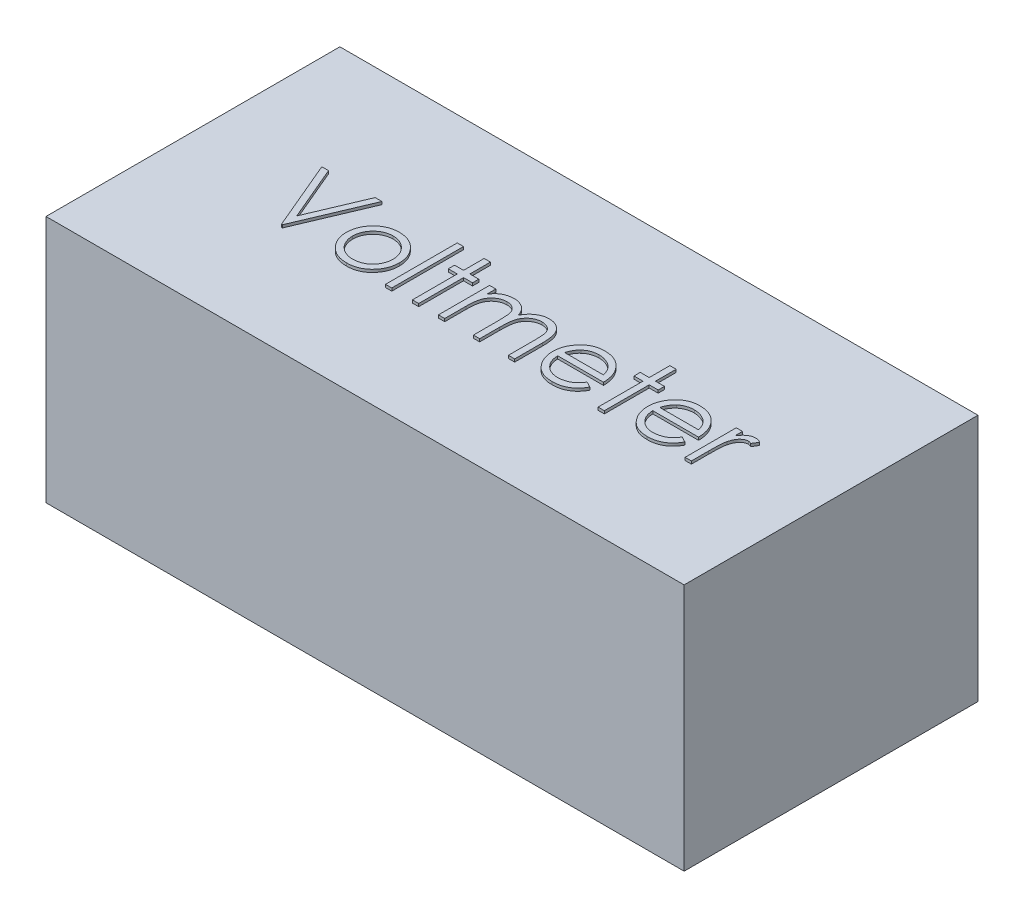
SolidWorks part; units mm, degrees
ref_plane "Front Plane" through (0, 0, 0) normal (0, 0, 1) x (1, 0, 0)
ref_plane "Top Plane" through (0, 0, 0) normal (0, 1, 0) x (1, 0, 0)
ref_plane "Right Plane" through (0, 0, 0) normal (1, 0, 0) x (0, 0, -1)
sketch "Sketch1" plane through (0, 0, 0) normal (0, 1, 0) x (1, 0, 0)
  line L1 (-14.0685, -2.1021) -> (8.7315, -2.1021)
  line L2 (-14.0685, -2.1021) -> (-14.0685, 8.3979)
  line L3 (-14.0685, 8.3979) -> (8.7315, 8.3979)
  line L4 (8.7315, -2.1021) -> (8.7315, 8.3979)
  dimension "D1" = 22.8
  dimension "D2" = 10.5
extrude "Boss-Extrude1" add sketch "Sketch1" along normal blind 8.86
sketch "Sketch2" plane through (0, 8.86, 0) normal (0, 1, 0) x (1, 0, 0)
  text T0 "Voltmeter" font "Century Gothic" height 2.5
  point P1 (-13.234, -0.8387)
  point P2 (-13.6832, -0.7826)
  point P3 (-14.0685, -0.9697)
  point P4 (-11.4559, 1.033)
  point P5 (-10.7447, 1.1827)
  point P6 (-14.0685, 1.1265)
  point P7 (-10.7073, 1.7629)
extrude "Boss-Extrude2" add sketch "Sketch2" along normal blind 0.1
